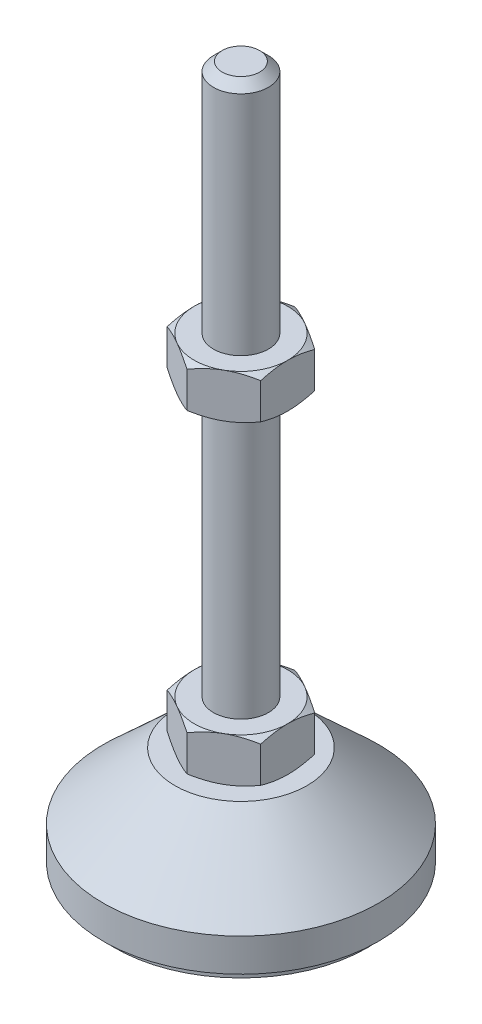
SolidWorks part; units mm, degrees
ref_plane "Спереди" through (0, 0, 0) normal (0, 0, 1) x (1, 0, 0)
ref_plane "Сверху" through (0, 0, 0) normal (0, 1, 0) x (1, 0, 0)
ref_plane "Справа" through (0, 0, 0) normal (1, 0, 0) x (0, 0, -1)
sketch "Эскиз1" plane through (0, 0, 0) normal (0, 0, 1) x (1, 0, 0)
  line L0 (0, 0) -> (-23, 0)
  line L1 (-23, 0) -> (-23, 2)
  line L2 (-23, 2) -> (-25, 2)
  line L3 (-25, 2) -> (-25, 8)
  line L4 (-25, 8) -> (-12, 20)
  line L5 (-12, 20) -> (-5, 20)
  line L12 (-5, 28) -> (-5, 126.4)
  line L13 (-5, 126.4) -> (-3.4, 128)
  line L14 (-3.4, 128) -> (0, 128)
  line L15 (0, 128) -> (0, 0) construction
  line L16 (-5, 20) -> (0, 20) construction
  line L17 (0, 0) -> (0, 128)
  line L18 (0, 0) -> (0, -7.9595) construction
  line L19 (-5, 28) -> (-5, 20)
  point P8 (-5, 77.2)
  point P23 (-8.5, 20)
  dimension "D1" = 10
  dimension "D2" = 20
  dimension "D3" = 8
  dimension "D4" = 50
  dimension "D5" = 5
  dimension "D6" = 1.6
  dimension "D7" = 45
  dimension "D8" = 24
  dimension "D9" = 2
  dimension "D10" = 100
  dimension "D11" = 6
revolve "Повернуть1" add sketch "Эскиз1" angle 360 about L17
sketch "Эскиз2" plane through (0, 20, 0) normal (0, 1, 0) x (1, 0, 0)
  line L1 (0, 9.815) -> (-8.5, 4.9075)
  line L2 (-8.5, 4.9075) -> (-8.5, -4.9075)
  line L3 (-8.5, -4.9075) -> (0, -9.815)
  line L4 (0, -9.815) -> (8.5, -4.9075)
  line L5 (8.5, -4.9075) -> (8.5, 4.9075)
  line L6 (8.5, 4.9075) -> (0, 9.815)
  circle A0 centre (0, 0) radius 8.5 construction
  dimension "D1" = 17
extrude "Бобышка-Вытянуть1" add sketch "Эскиз2" along normal up to vertex (8 mm away) up to point (-5, 28, 0)
ref_plane "Плоскость1" through (0, 77.2, 0) normal (0, 1, 0) x (1, 0, 0)
sketch "Эскиз3" plane through (0, 77.2, 0) normal (0, 1, 0) x (1, 0, 0)
  line L6 (8.5, 4.9075) -> (0, 9.815)
  line L7 (0, 9.815) -> (-8.5, 4.9075)
  line L8 (-8.5, 4.9075) -> (-8.5, -4.9075)
  line L9 (-8.5, -4.9075) -> (0, -9.815)
  line L10 (0, -9.815) -> (8.5, -4.9075)
  line L11 (8.5, -4.9075) -> (8.5, 4.9075)
  line L12 (8.5, 4.9075) -> (0, 9.815)
  line L13 (0, 9.815) -> (-8.5, 4.9075)
  line L14 (-8.5, 4.9075) -> (-8.5, -4.9075)
  line L15 (-8.5, -4.9075) -> (0, -9.815)
  line L16 (0, -9.815) -> (8.5, -4.9075)
  line L17 (8.5, -4.9075) -> (8.5, 4.9075)
  dimension "D1" = 0
extrude "Бобышка-Вытянуть2" add sketch "Эскиз3" along normal blind 8
sketch "Эскиз4" plane through (0, 0, 0) normal (0, 0, 1) x (1, 0, 0)
  line L0 (-8.5, 85.2) -> (-15.4282, 81.2)
  line L1 (-15.4282, 81.2) -> (-15.4282, 85.2)
  line L2 (-15.4282, 85.2) -> (-8.5, 85.2)
  line L3 (-15.4282, 81.2) -> (-8.5, 77.2)
  line L4 (50, 77.2) -> (-50, 77.2) construction
  line L5 (-8.5, 77.2) -> (-15.4282, 77.2)
  line L6 (-15.4282, 77.2) -> (-15.4282, 81.2)
  line L7 (-8.5, 85.2) -> (-8.5, 77.2) construction
  line L8 (-8.5, 28) -> (-15.4282, 28)
  line L9 (-15.4282, 28) -> (-15.4282, 24)
  line L10 (-15.4282, 24) -> (-8.5, 28)
  line L11 (-8.5, 20) -> (-15.4282, 24)
  line L12 (-15.4282, 24) -> (-15.4282, 20)
  line L13 (-15.4282, 20) -> (-8.5, 20)
  line L14 (0, 128) -> (0, 96.3793) construction
  dimension "D1" = 30
  dimension "D2" = 30
revolve "Вырез-Повернуть2" cut sketch "Эскиз4" angle 360 about L14
